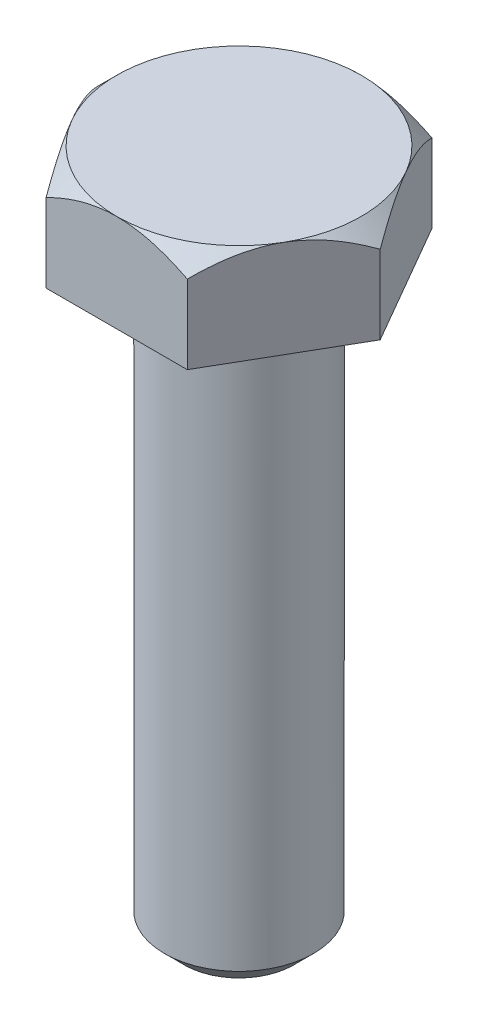
SolidWorks part; units mm, degrees
ref_plane "Спереди" through (0, 0, 0) normal (0, 0, 1) x (1, 0, 0)
ref_plane "Сверху" through (0, 0, 0) normal (0, 1, 0) x (1, 0, 0)
ref_plane "Справа" through (0, 0, 0) normal (1, 0, 0) x (0, 0, -1)
sketch "Эскиз6" plane through (0, 0, 0) normal (0, 1, 0) x (1, 0, 0)
  line L1 (7.25, 0) -> (3.625, 6.2787)
  line L2 (3.625, 6.2787) -> (-3.625, 6.2787)
  line L3 (-3.625, 6.2787) -> (-7.25, 0)
  line L4 (-7.25, 0) -> (-3.625, -6.2787)
  line L5 (-3.625, -6.2787) -> (3.625, -6.2787)
  line L6 (3.625, -6.2787) -> (7.25, 0)
  circle A0 centre (0, 0) radius 6.2787 construction
  dimension "D1" = 14.5
extrude "Бобышка-Вытянуть1" add sketch "Эскиз6" along normal blind 5
sketch "Эскиз8" plane through (0, 5, 0) normal (0, 1, 0) x (1, 0, 0)
  circle A0 centre (0, 0) radius 6.2787
extrude "Вырез-Вытянуть1" cut sketch "Эскиз8" against normal blind 1 draft 45 flip side to cut
sketch "Эскиз9" plane through (0, 0, 0) normal (0, -1, 0) x (1, 0, 0)
  circle A0 centre (0, 0) radius 3.825
  dimension "D1" = 7.65
extrude "bolt length" add sketch "Эскиз9" along normal blind 30
fillet "Скругление1" radius 1 1 edges at (0, 0, 3.825)
chamfer "Фаска1" distance 1 angle 45 1 edges at (0, -30, -3.825)
